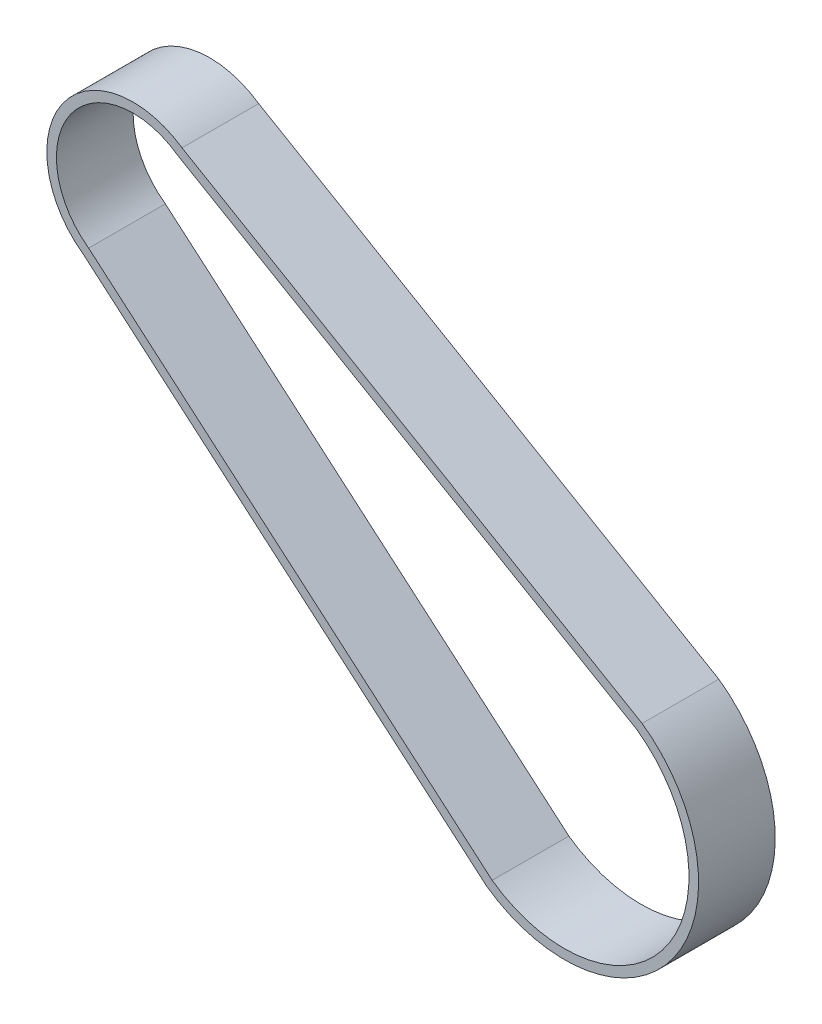
SolidWorks part; units mm, degrees
ref_plane "Plan de face" through (0, 0, 0) normal (0, 0, 1) x (1, 0, 0)
ref_plane "Plan de dessus" through (0, 0, 0) normal (0, 1, 0) x (1, 0, 0)
ref_plane "Plan de droite" through (0, 0, 0) normal (1, 0, 0) x (0, 0, -1)
sketch "Esquisse1" plane through (0, 0, 0) normal (0, 0, 1) x (1, 0, 0)
  line L0 (0, 0) -> (0, -18) construction
  line L1 (0, -18) -> (-45, -18) construction
  line L20 (-45, -18) -> (-45, 32) construction
  line L21 (-49.6362, 25.4804) -> (-45, 32) construction
  line L22 (-45, 32) -> (0, 0) construction
  line L23 (0, 0) -> (-8.1133, -11.4094) construction
  line L24 (0, 0) -> (-45, 32) construction
  line L26 (-45, 32) -> (-50.2157, 24.6654) construction
  line L28 (-49.6362, 25.4804) -> (-40.3638, 38.5196) construction
  line L29 (-50.2157, 24.6654) -> (-49.6362, 25.4804) construction
  line L30 (0, 0) -> (8.1133, 11.4094) construction
  line L31 (-40.3638, 38.5196) -> (-39.8926, 39.4104) construction
  line L32 (-8.1133, -11.4094) -> (-7.5338, -10.5944) construction
  line L33 (-7.5338, -10.5944) -> (7.5338, 10.5944) construction
  line L34 (7.5338, 10.5944) -> (8.1133, 11.4094) construction
  line L35 (-40.3638, 38.5196) -> (7.5338, 10.5944)
  line L36 (-49.6362, 25.4804) -> (-7.5338, -10.5944)
  line L37 (-39.8926, 39.4104) -> (8.1133, 11.4094)
  line L38 (-50.2157, 24.6654) -> (-8.1133, -11.4094)
  circle A8 centre (0, 0) radius 13 construction
  circle A9 centre (-45, 32) radius 9 construction
  circle A10 centre (0, 0) radius 14 construction
  circle A11 centre (-45, 32) radius 8 construction
  arc A12 (-50.2157, 24.6654) -> (-39.7843, 39.3346) centre (-45, 32) cw
  arc A13 (-49.6362, 25.4804) -> (-40.3638, 38.5196) centre (-45, 32) cw
  arc A14 (7.5338, 10.5944) -> (-7.5338, -10.5944) centre (0, 0) cw
  arc A15 (-8.1133, -11.4094) -> (8.1133, 11.4094) centre (0, 0) ccw
extrude "Boss.-Extru.1" add sketch "Esquisse1" along normal blind 8
